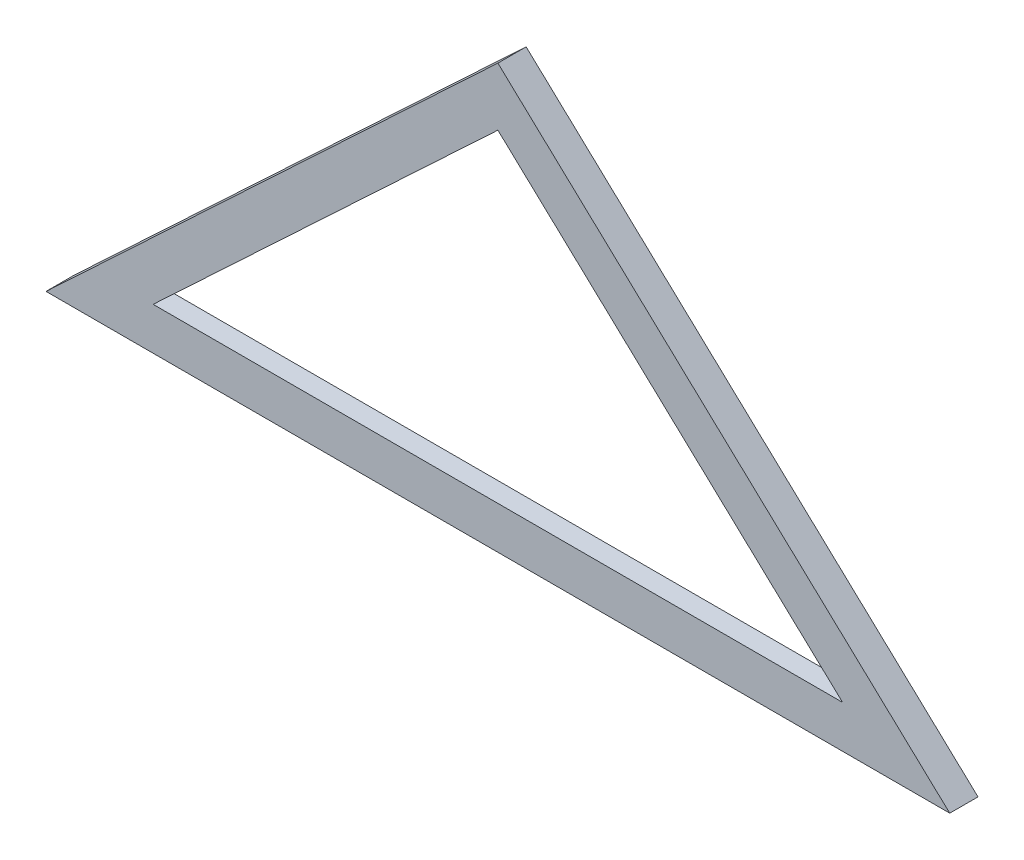
SolidWorks part; units mm, degrees
ref_plane "Alzado" through (0, 0, 0) normal (0, 0, 1) x (1, 0, 0)
ref_plane "Planta" through (0, 0, 0) normal (0, 1, 0) x (1, 0, 0)
ref_plane "Vista lateral" through (0, 0, 0) normal (1, 0, 0) x (0, 0, -1)
sketch "Croquis1" plane through (0, 0, 0) normal (0, 0, 1) x (1, 0, 0)
  line L0 (0, 0) -> (320, 0)
  line L1 (160, 0) -> (160, 150) construction
  line L2 (0, 0) -> (160, 150)
  line L3 (160, 150) -> (320, 0)
  line L4 (160, 129.439) -> (282.0683, 15)
  line L5 (37.9317, 15) -> (282.0683, 15)
  line L6 (37.9317, 15) -> (160, 129.439)
  dimension "D1" = 320
  dimension "D2" = 150
  dimension "D3" = 15
extrude "Saliente-Extruir1" add sketch "Croquis1" along normal blind 10
sketch "Croquis2" plane through (0, 0, 0) normal (0, 0, -1) x (-1, 0, 0)
  line L0 (0, 0) -> (-160, 150) construction
  line L1 (-160, 150) -> (-320, 0) construction
  line L2 (-320, 0) -> (0, 0) construction
  line L3 (-294.7122, 10) -> (-25.2878, 10)
  line L4 (-25.2878, 10) -> (-160, 136.2927)
  line L5 (-160, 136.2927) -> (-294.7122, 10)
  dimension "D1" = 10
extrude "Cortar-Extruir1" cut sketch "Croquis2" against normal blind 3
